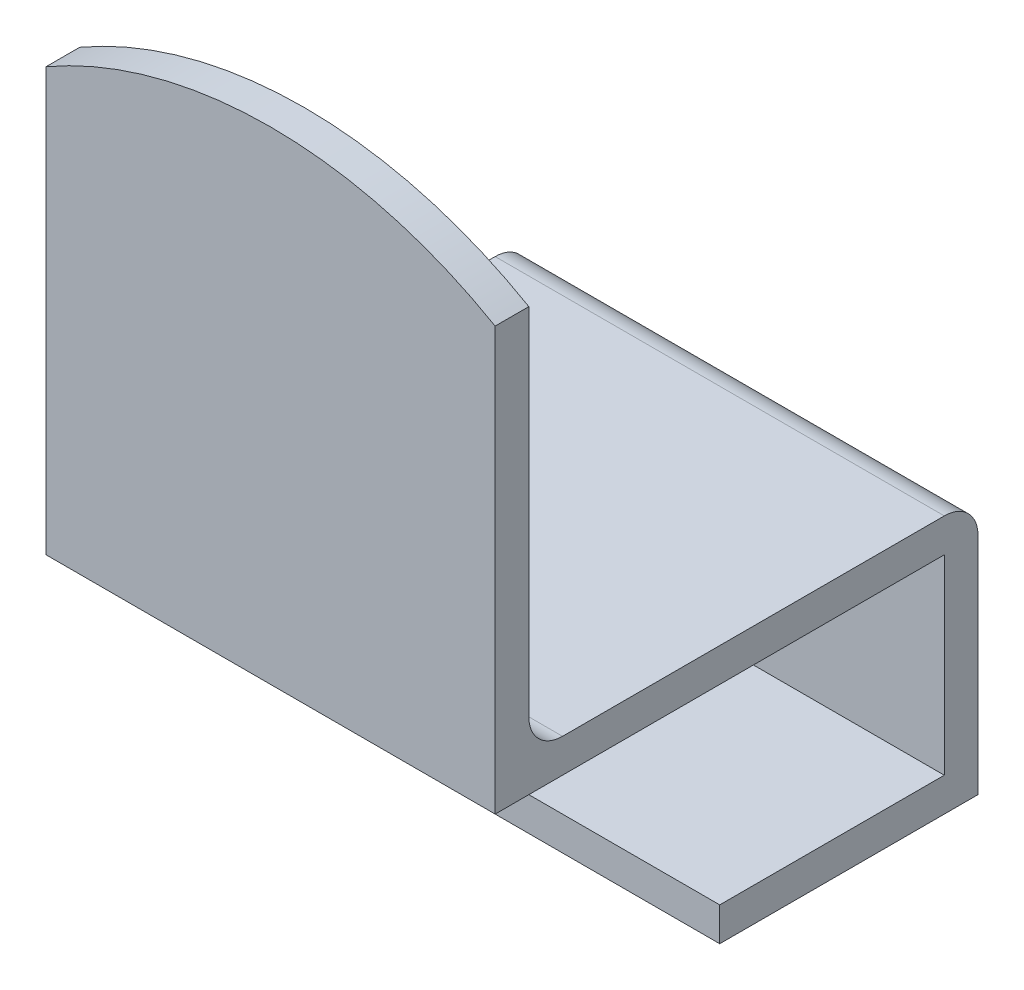
SolidWorks part; units mm, degrees
ref_plane "Front Plane" through (0, 0, 0) normal (0, 0, 1) x (1, 0, 0)
ref_plane "Top Plane" through (0, 0, 0) normal (0, 1, 0) x (1, 0, 0)
ref_plane "Right Plane" through (0, 0, 0) normal (1, 0, 0) x (0, 0, -1)
sketch "Sketch1" plane through (0, 0, 0) normal (0, 1, 0) x (1, 0, 0)
  line L1 (-20, -20) -> (20, -20)
  line L2 (-20, -20) -> (-20, 20)
  line L3 (-20, 20) -> (20, 20)
  line L4 (20, -20) -> (20, 20)
  line L5 (-20, -20) -> (20, 20) construction
  line L6 (-20, 20) -> (20, -20) construction
  point P0 (0, 0)
  dimension "D1" = 40
  dimension "D2" = 40
extrude "Boss-Extrude1" add sketch "Sketch1" along normal blind 3 contours L3 L4 L1 L2
sketch "Sketch2" plane through (0, 0, 0) normal (0, 1, 0) x (1, 0, 0)
  line L1 (20, -20) -> (-20, -20)
  line L2 (20, -20) -> (20, -23)
  line L3 (20, -23) -> (-20, -23)
  line L4 (-20, -20) -> (-20, -23)
  dimension "D1" = 40
  dimension "D2" = 3
extrude "Boss-Extrude2" add sketch "Sketch2" along normal blind 53
sketch "Sketch3" plane through (0, 0, 0) normal (0, -1, 0) x (1, 0, 0)
  line L0 (20, 23) -> (20, -20) construction
  line L1 (-20, -20) -> (20, -20)
  line L2 (-20, -20) -> (-20, -17)
  line L3 (-20, -17) -> (20, -17)
  line L4 (20, -20) -> (20, -17)
  dimension "D1" = 3
extrude "Boss-Extrude3" add sketch "Sketch3" along normal blind 20
sketch "Sketch4" plane through (0, 0, 20) normal (0, 0, -1) x (-1, 0, 0)
  line L0 (20, 3) -> (-20, 3) construction
  line L1 (20, 53) -> (20, 3) construction
  line L2 (-20, 53) -> (-20, 3) construction
  line L3 (7.2681, 10.3729) -> (-47.2681, 64.9091) construction
  line L4 (16.7813, 52.078) -> (23.2187, 23.204) construction
  line L5 (-20, 37.641) -> (-20, 53)
  line L6 (-20, 53) -> (20, 53)
  line L7 (20, 53) -> (20, 37.641)
  arc A0 (20, 37.641) -> (-20, 37.641) centre (0, 3) ccw
  point P2 (-20, 37.641)
  point P8 (20, 37.641)
  dimension "D1" = 80
extrude "Cut-Extrude1" cut sketch "Sketch4" against normal up to next
fillet "Fillet1" radius 3 2 edges at (0, 3, 20) (0, 3, -20)
sketch "Sketch5" plane through (0, 0, -17) normal (0, 0, 1) x (1, 0, 0)
  line L1 (20, -20) -> (-20, -20) construction
  line L2 (20, -20) -> (-20, -20)
  line L3 (-20, -20) -> (-20, -17)
  line L4 (-20, -20) -> (-20, 0) construction
  line L5 (-20, -17) -> (20, -17)
  line L6 (20, -20) -> (20, 0) construction
  line L7 (20, -17) -> (20, -20)
  dimension "D1" = 3
extrude "Boss-Extrude4" add sketch "Sketch5" along normal blind 20
